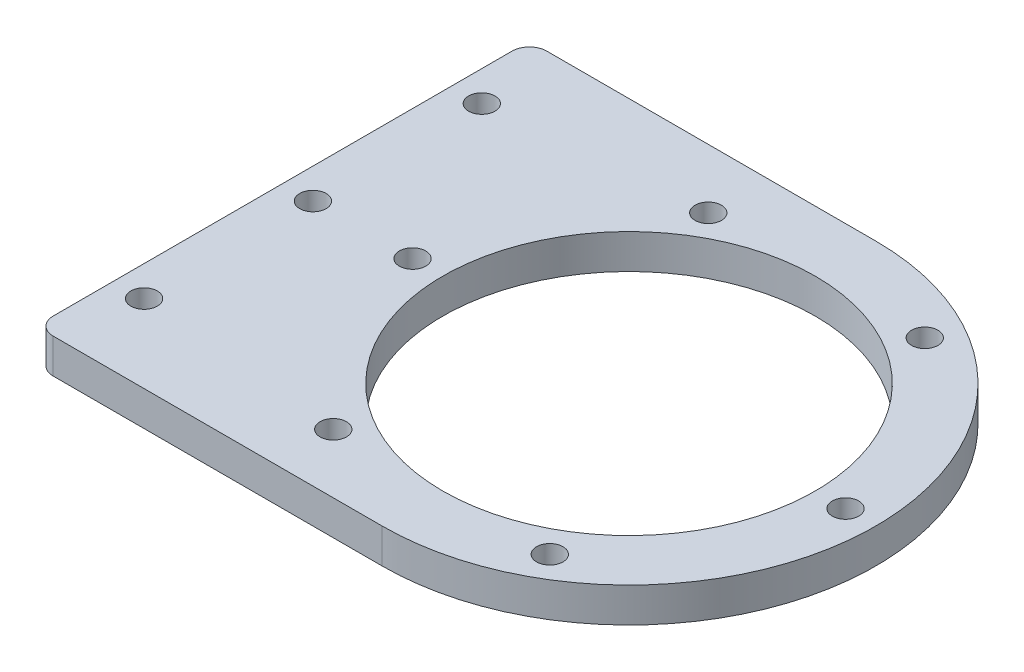
SolidWorks part; units mm, degrees
material "Thornel Mat VMA"
ref_plane "前视基准面" through (0, 0, 0) normal (0, 0, 1) x (1, 0, 0)
ref_plane "上视基准面" through (0, 0, 0) normal (0, 1, 0) x (1, 0, 0)
ref_plane "右视基准面" through (0, 0, 0) normal (1, 0, 0) x (0, 0, -1)
other "Configuration Table"
sketch "草图1" plane through (0, 0, 0) normal (0, 1, 0) x (1, 0, 0)
  line L1 (-19.5, -28.5) -> (19.5, -28.5)
  line L2 (-19.5, -28.5) -> (-19.5, 28.5)
  line L3 (-19.5, 28.5) -> (19.5, 28.5)
  line L4 (19.5, -28.5) -> (19.5, 28.5)
  line L5 (-19.5, -28.5) -> (19.5, 28.5) construction
  line L6 (-19.5, 28.5) -> (19.5, -28.5) construction
  circle A0 centre (19.5, 0) radius 28.5
  point P0 (0, 0)
  dimension "D1" = 57
  dimension "D2" = 39
extrude "凸台-拉伸1" add sketch "草图1" along normal blind 4 contours L4 A0 | A0 L3 L2 L1 | L4 A0
sketch "草图2" plane through (0, 4, 0) normal (0, 1, 0) x (1, 0, 0)
  circle A0 centre (19.5, 0) radius 21.5
  dimension "D1" = 43
extrude "切除-拉伸1" cut sketch "草图2" against normal through all
sketch "草图4" plane through (0, 4, 0) normal (0, 1, 0) x (1, 0, 0)
  circle A0 centre (19.5, 0) radius 25 construction
  circle A1 centre (-5.5, 0) radius 1.525
  circle A2 centre (7, 21.6506) radius 1.525
  circle A3 centre (32, 21.6506) radius 1.525
  circle A4 centre (44.5, 0) radius 1.525
  circle A5 centre (32, -21.6506) radius 1.525
  circle A6 centre (7, -21.6506) radius 1.525
  point P17 (19.5, 0)
  dimension "D1" = 50
  dimension "D2" = 3.05
  dimension "D3" = 6
extrude "切除-拉伸3" cut sketch "草图4" against normal through all
sketch "草图5" plane through (0, 4, 0) normal (0, 1, 0) x (1, 0, 0)
  circle A6 centre (-17, 19.5) radius 1.525
  circle A7 centre (-17, 0) radius 1.525
  circle A8 centre (-17, -19.5) radius 1.525
  circle A9 centre (-17, 19.5) radius 1.25 construction
  circle A10 centre (-17, 0) radius 1.25 construction
  circle A11 centre (-17, -19.5) radius 1.25 construction
  dimension "D1" = 3.05
extrude "切除-拉伸4" cut sketch "草图5" against normal through all
sketch "草图6" plane through (0, 4, 0) normal (0, 1, 0) x (1, 0, 0)
  line L0 (-19.5, -28.5) -> (19.5, -28.5) construction
  line L1 (-19.5, 28.5) -> (-20.5, 28.5)
  line L2 (-19.5, 28.5) -> (-19.5, -28.5)
  line L3 (-19.5, -28.5) -> (-20.5, -28.5)
  line L4 (-20.5, 28.5) -> (-20.5, -28.5)
  dimension "D1" = 1
extrude "凸台-拉伸2" add sketch "草图6" against normal up to surface (4 mm away) up to face at (-17, 0, -17.975)
fillet "圆角1" radius 2 2 edges at (-20.5, 2, -28.5) (-20.5, 2, 28.5)
